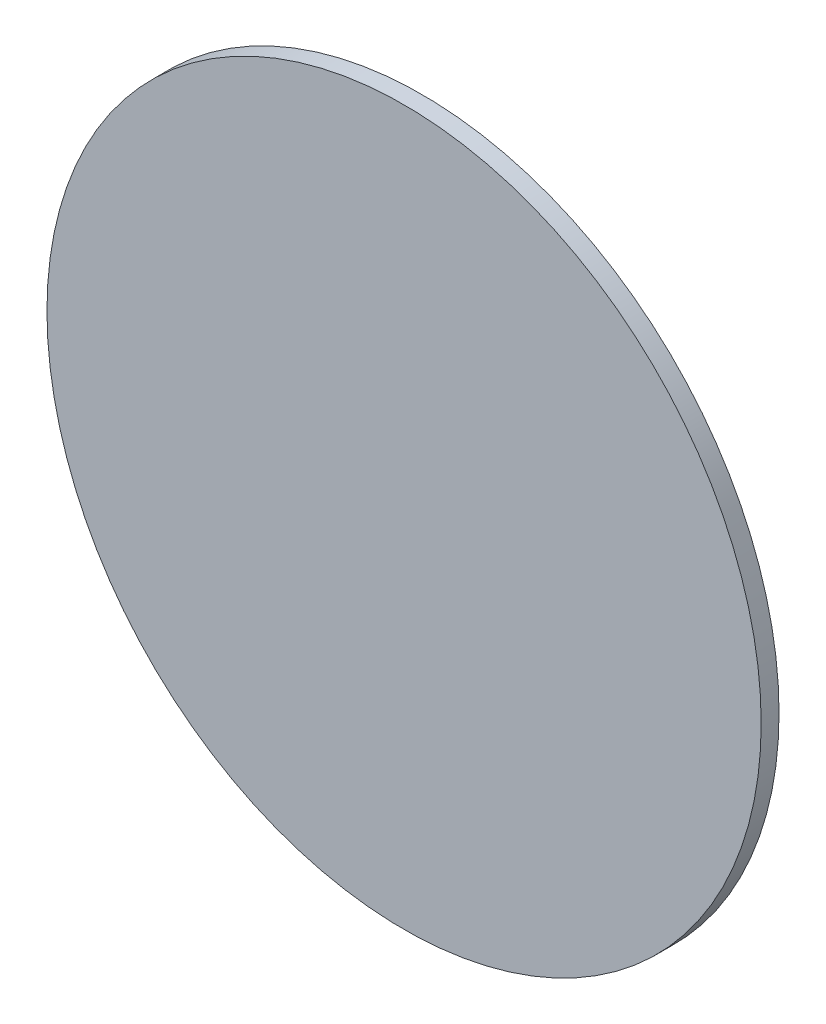
SolidWorks part; units mm, degrees
ref_plane "Front" through (0, 0, 0) normal (0, 0, 1) x (1, 0, 0)
ref_plane "Top" through (0, 0, 0) normal (0, 1, 0) x (1, 0, 0)
ref_plane "Right" through (0, 0, 0) normal (1, 0, 0) x (0, 0, -1)
sketch "草图1" plane through (0, 0, 0) normal (0, 0, 1) x (1, 0, 0)
  circle A0 centre (0, 0) radius 10
  dimension "D1" = 20
extrude "凸台-拉伸1" add sketch "草图1" along normal blind 0.5
